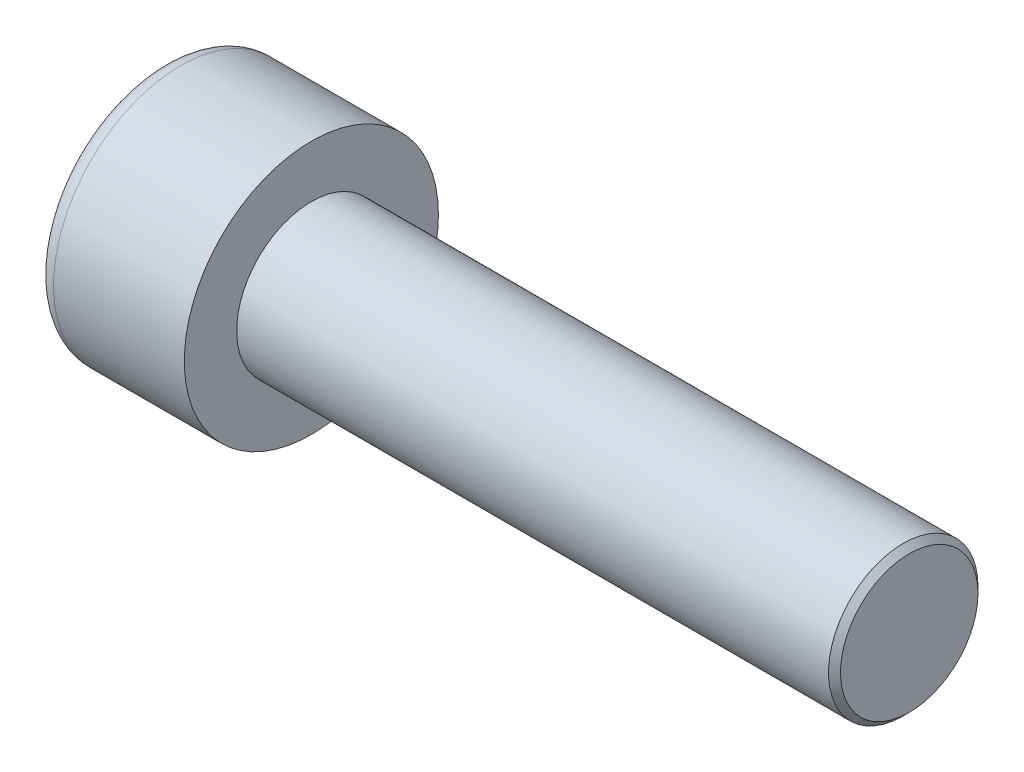
SolidWorks part; units mm, degrees
ref_plane "Front" through (0, 0, 0) normal (0, 0, 1) x (1, 0, 0)
ref_plane "Top" through (0, 0, 0) normal (0, 1, 0) x (1, 0, 0)
ref_plane "Right" through (0, 0, 0) normal (1, 0, 0) x (0, 0, -1)
sketch "Sketch1" plane through (0, 0, 0) normal (1, 0, 0) x (0, 0, -1)
  circle A0 centre (0, 0) radius 4.25
  dimension "dk" = 8.5
extrude "BaseHead" add sketch "Sketch1" along normal blind 5
sketch "Sketch2" plane through (5, 0, 0) normal (1, 0, 0) x (0, 0, -1)
  circle A0 centre (0, 0) radius 2.5
  dimension "d" = 5
extrude "BaseBody" add sketch "Sketch2" along normal blind 20
cosmetic thread "ThreadCosmetic1" [suppressed] parameters "b"=22, "D2"=4.134
sketch "Sketch3" plane through (0, 0, 0) normal (1, 0, 0) x (0, 0, -1)
  line L1 (2.3094, 0) -> (1.1547, 2)
  line L2 (1.1547, 2) -> (-1.1547, 2)
  line L3 (-1.1547, 2) -> (-2.3094, 0)
  line L4 (-2.3094, 0) -> (-1.1547, -2)
  line L5 (-1.1547, -2) -> (1.1547, -2)
  line L6 (1.1547, -2) -> (2.3094, 0)
  circle A0 centre (0, 0) radius 2 construction
  dimension "s" = 4
  dimension "e" = 4.6188
extrude "HexagonSocket" cut sketch "Sketch3" along normal blind 2.5
sketch "Sketch4" plane through (-4.1961, 0.75, 0) normal (0, 0, 1) x (-1, 0, 0)
  line L0 (-6.6961, 2.75) -> (-7.8508, 0.75)
  line L2 (-7.8508, 0.75) -> (-6.6961, 0.75)
  line L3 (-6.6961, 0.75) -> (-6.6961, 2.75)
  line L4 (-5.0351, 0.75) -> (0.839, 0.75) construction
  line L5 (-29.1961, 0.75) -> (-9.1961, 0.75) construction
  line L6 (-9.1961, 0.75) -> (-4.1961, 0.75) construction
  dimension "m" = 60
revolve "Cut-Revolve1" cut sketch "Sketch4" angle 360 about L4
fillet "HeadFillet" [suppressed] radius 0.2
fillet "TopFillet" radius 0.625 1 edges at (0, 0, -4.25)
chamfer "Chamfer1" distance 0.2 angle 45 1 edges at (25, 0, -2.5)
sketch "Sketch5" plane through (0, 0, 0) normal (0, 0, 1) x (1, 0, 0)
  line L0 (24.8, 2.125) -> (25.0165, 2.5)
  line L1 (25.0165, 2.5) -> (25.0165, 2.933)
  line L2 (25.0165, 2.933) -> (24.5835, 2.933)
  line L3 (24.5835, 2.933) -> (24.5835, 2.5)
  line L4 (24.5835, 2.5) -> (24.8, 2.125)
  line L5 (0, 0) -> (7.8886, 0) construction
  line L6 (24.8, -2.5) -> (24.8, 2.5) construction
  dimension "D1" = 5
  dimension "D2" = 0.433
revolve "Cut-Revolve10" [suppressed] cut sketch "Sketch5" angle 360 about L5
pattern_linear "LPattern10" [suppressed] count 42 spacing 0.5196 along (1, 0, 0)
equation "\"r1@TopFillet\" = \"d@Sketch2\" / 8"
equation "\"D1@Chamfer1\" = \"r@HeadFillet\""
equation "\"D1@Sketch5\" = \"d@Sketch2\""
equation "\"D2@Sketch5\" =  ( \"d@Sketch2\" - \"D2@ThreadCosmetic1\" )  / 2"
equation "\"D3@LPattern10\" = \"D2@Sketch5\" * 1.2"
equation "\"D1@LPattern10\" = \"b@ThreadCosmetic1\" / \"D3@LPattern10\""
